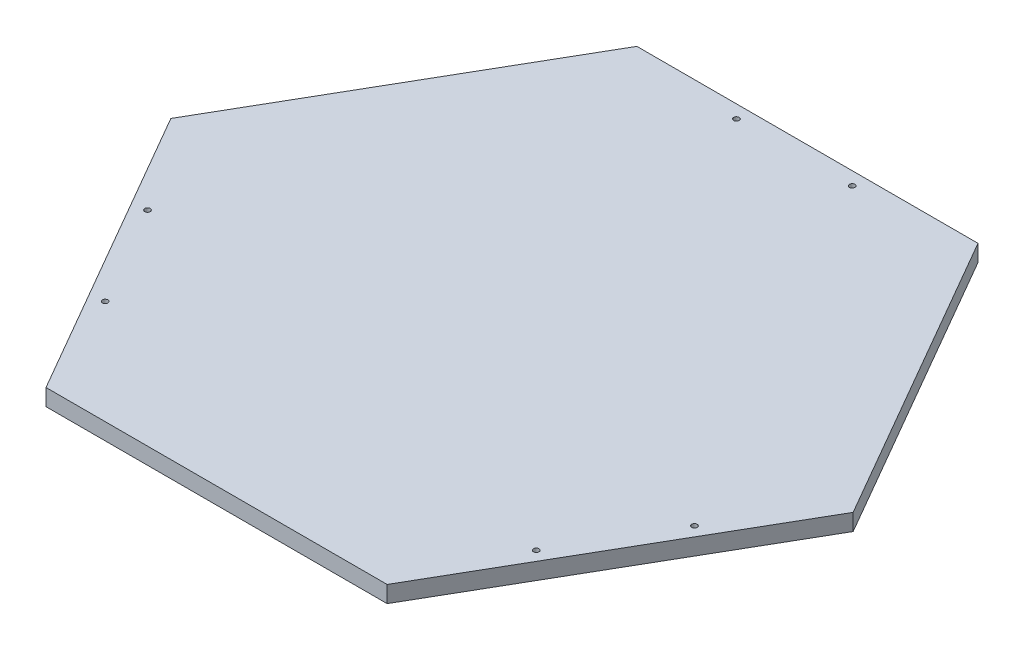
SolidWorks part; units mm, degrees
ref_plane "Front Plane" through (0, 0, 0) normal (0, 0, 1) x (1, 0, 0)
ref_plane "Top Plane" through (0, 0, 0) normal (0, 1, 0) x (1, 0, 0)
ref_plane "Right Plane" through (0, 0, 0) normal (1, 0, 0) x (0, 0, -1)
sketch "Sketch1" plane through (0, 0, 0) normal (0, 1, 0) x (1, 0, 0)
  line L0 (130.2076, -225.5261) -> (260.4152, 0)
  line L1 (-152.4, -152.4) -> (152.4, -152.4) construction
  line L2 (-152.4, -152.4) -> (-152.4, 152.4) construction
  line L3 (-152.4, 152.4) -> (152.4, 152.4) construction
  line L4 (152.4, -152.4) -> (152.4, 152.4) construction
  line L5 (-152.4, -152.4) -> (152.4, 152.4) construction
  line L6 (-152.4, 152.4) -> (152.4, -152.4) construction
  line L7 (124.4341, 215.5261) -> (-124.4341, 215.5261) construction
  line L8 (-124.4341, 215.5261) -> (-248.8682, 0) construction
  line L9 (-248.8682, 0) -> (-124.4341, -215.5261) construction
  line L10 (-124.4341, -215.5261) -> (124.4341, -215.5261) construction
  line L11 (124.4341, -215.5261) -> (248.8682, 0) construction
  line L12 (248.8682, 0) -> (124.4341, 215.5261) construction
  line L13 (260.4152, 0) -> (130.2076, 225.5261)
  line L14 (130.2076, 225.5261) -> (-130.2076, 225.5261)
  line L15 (-130.2076, 225.5261) -> (-260.4152, 0)
  line L16 (-260.4152, 0) -> (-130.2076, -225.5261)
  line L17 (-130.2076, -225.5261) -> (130.2076, -225.5261)
  circle A0 centre (0, 0) radius 215.5261 construction
  circle A1 centre (0, 0) radius 215.5261 construction
  point P0 (0, 0)
  dimension "D2" = 431.0523
  dimension "D1" = 304.8
  dimension "D3" = 10
extrude "Boss-Extrude1" add sketch "Sketch1" along normal blind 12.7
sketch "Sketch2" plane through (0, 12.7, 0) normal (0, 1, 0) x (1, 0, 0)
  line L0 (-130.2076, 225.5261) -> (-130.2076, 215.5261) construction
  line L1 (-44.2076, 225.5261) -> (-44.2076, 215.5261) construction
  line L2 (130.2076, 225.5261) -> (-130.2076, 225.5261) construction
  line L3 (44.2076, 225.5261) -> (44.2076, 215.5261) construction
  line L4 (0, 225.5261) -> (0, 215.5261) construction
  line L5 (-130.2076, 215.5261) -> (44.2076, 215.5261) construction
  line L6 (-195.3114, -112.7631) -> (-165.9999, -95.8401) construction
  line L7 (-260.4152, 0) -> (-130.2076, -225.5261) construction
  line L8 (195.3114, -112.7631) -> (171.5615, -99.0511) construction
  line L9 (130.2076, -225.5261) -> (260.4152, 0) construction
  line L10 (121.5473, -220.5261) -> (208.7549, -69.4782) construction
  line L11 (195.3114, -112.7631) -> (186.6511, -107.7631) construction
  line L12 (217.4152, -74.4782) -> (208.7549, -69.4782) construction
  line L13 (173.2076, -151.048) -> (164.5473, -146.048) construction
  line L14 (130.2076, -225.5261) -> (121.5473, -220.5261) construction
  line L15 (-251.7549, 5) -> (-164.5473, -146.048) construction
  line L16 (-195.3114, -112.7631) -> (-186.6511, -107.7631) construction
  line L17 (-173.2076, -151.048) -> (-164.5473, -146.048) construction
  line L18 (-217.4152, -74.4782) -> (-208.7549, -69.4782) construction
  line L19 (-260.4152, 0) -> (-251.7549, 5) construction
  point P12 (0, 225.5261)
  dimension "D1" = 86
  dimension "D2" = 10
hole_wizard "Tap Drill for M5x0.8 Tap1" positions "Sketch4" profile "Sketch3" hole size "M5x0.8" standard "ANSI Metric" end condition through all
sketch "Sketch4" plane through (0, 12.7, 0) normal (0, 1, 0) x (1, 0, 0)
  point P0 (-44.2076, 215.5261)
  point P3 (44.2076, 215.5261)
  point P6 (-208.7549, -69.4782)
  point P9 (-164.5473, -146.048)
  point P12 (164.5473, -146.048)
  point P15 (208.7549, -69.4782)
sketch "Sketch3" plane through (-44.2076, 12.7, -215.5261) normal (1, 0, 0) x (0, 0, 1)
  line L0 (0, 0) -> (0, 12.7)
  line L1 (0, 12.7) -> (2.1, 12.7)
  line L2 (2.1, 12.7) -> (2.1, 0)
  line L5 (2.1, 0) -> (0, 0)
  line L11 (0, -6.35) -> (0, 107.95) construction
  dimension "Thru Hole Dia." = 4.2
  dimension "Thru Hole Depth" = 12.7
